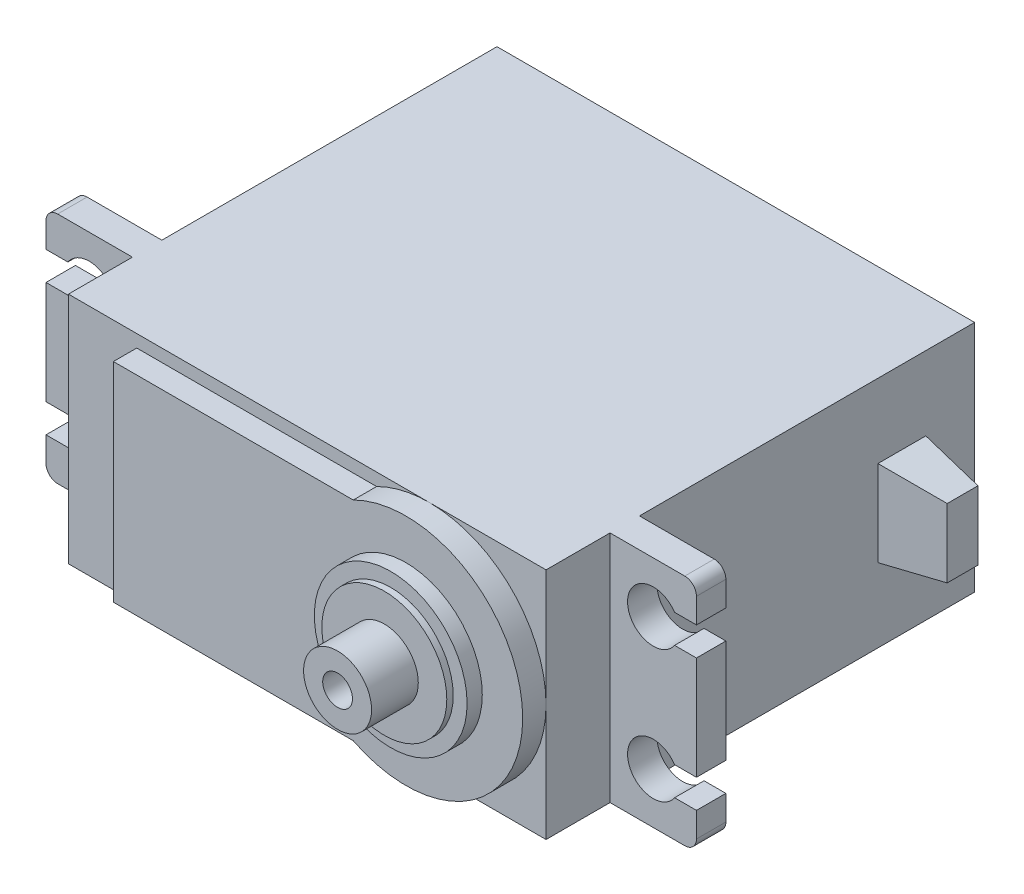
SolidWorks part; units mm, degrees
ref_plane "정면" through (0, 0, 0) normal (0, 0, 1) x (1, 0, 0)
ref_plane "윗면" through (0, 0, 0) normal (0, 1, 0) x (1, 0, 0)
ref_plane "우측면" through (0, 0, 0) normal (1, 0, 0) x (0, 0, -1)
sketch "스케치1" plane through (0, 0, 0) normal (0, 0, 1) x (1, 0, 0)
  line L1 (20.45, -10) -> (-20.45, -10)
  line L2 (20.45, -10) -> (20.45, 10)
  line L3 (20.45, 10) -> (-20.45, 10)
  line L4 (-20.45, -10) -> (-20.45, 10)
  line L5 (20.45, -10) -> (-20.45, 10) construction
  line L6 (20.45, 10) -> (-20.45, -10) construction
  point P0 (0, 0)
extrude "보스-돌출1" add sketch "스케치1" along normal blind 36.7
sketch "스케치2" plane through (0, 0, 36.7) normal (0, 0, 1) x (1, 0, 0)
  line L0 (20.45, -10) -> (20.45, 10) construction
  circle A0 centre (10.45, 0) radius 10
  dimension "D1" = 10
extrude "보스-돌출2" add sketch "스케치2" along normal blind 2
sketch "스케치3" plane through (0, 0, 38.7) normal (0, 0, 1) x (1, 0, 0)
  circle A0 centre (10.45, 0) radius 6.54
extrude "보스-돌출3" add sketch "스케치3" along normal blind 1.3
sketch "스케치4" plane through (0, 0, 40) normal (0, 0, 1) x (1, 0, 0)
  circle A0 centre (10.45, 0) radius 5.35
extrude "보스-돌출4" add sketch "스케치4" along normal blind 0.55
sketch "스케치5" plane through (0, 0, 40.55) normal (0, 0, 1) x (1, 0, 0)
  circle A1 centre (10.45, 0) radius 2.91
  circle A2 centre (10.45, 0) radius 1.275
extrude "보스-돌출5" add sketch "스케치5" along normal blind 4
sketch "스케치6" plane through (0, 0, 36.7) normal (0, 0, 1) x (1, 0, 0)
  line L0 (5.9395, 8.925) -> (-14.6, 8.925)
  line L1 (-14.6, 8.925) -> (-14.6, -8.925)
  line L2 (0.45, 0) -> (-14.6, 0) construction
  line L3 (5.9395, -8.925) -> (-14.6, -8.925)
  circle A0 centre (10.45, 0) radius 10 construction
  arc A2 (10.45, 10) -> (10.45, -10) centre (10.45, 0) ccw construction
  arc A3 (5.9395, 8.925) -> (5.9395, -8.925) centre (10.45, 0) ccw
  dimension "D1" = 5.85
  dimension "D2" = 17.85
extrude "보스-돌출6" add sketch "스케치6" along normal blind 2
sketch "스케치7" plane through (20.45, 0, 0) normal (1, 0, 0) x (0, 0, -1)
  line L0 (-36.7, -10) -> (0, -10) construction
  line L1 (-31.22, -10) -> (-28.7, -10)
  line L2 (-31.22, -10) -> (-31.22, 10)
  line L3 (-31.22, 10) -> (-28.7, 10)
  line L4 (-28.7, -10) -> (-28.7, 10)
  line L5 (-36.7, 10) -> (0, 10) construction
  line L6 (0, -10) -> (0, 10) construction
  dimension "D1" = 28.7
extrude "보스-돌출7" add sketch "스케치7" along normal blind 7.4
sketch "스케치8" plane through (0, 0, 31.22) normal (0, 0, 1) x (1, 0, 0)
  line L0 (27.85, 0) -> (20.45, 0) construction
  line L1 (27.85, 10) -> (27.85, -10) construction
  line L2 (20.45, 10) -> (20.45, -10) construction
  line L3 (24.15, 10) -> (24.15, 7.85) construction
  line L4 (27.85, 10) -> (20.45, 10) construction
  line L5 (27.85, 6.875) -> (27.85, 4.425)
  line L6 (27.85, -4.425) -> (27.85, -6.875)
  line L7 (27.85, 6.875) -> (25.9774, 6.875)
  line L9 (27.85, 4.425) -> (25.9774, 4.425)
  line L10 (27.85, -6.875) -> (25.9774, -6.875)
  line L11 (27.85, -4.425) -> (25.9774, -4.425)
  arc A0 (25.9774, 6.875) -> (25.9774, 4.425) centre (24.15, 5.65) ccw
  arc A1 (25.9774, -6.875) -> (25.9774, -4.425) centre (24.15, -5.65) cw
  dimension "D1" = 2.2
extrude "컷-돌출3" cut sketch "스케치8" against normal blind 3.4
fillet "필렛1" radius 1 2 edges at (27.85, 10, 29.96) (27.85, -10, 29.96)
mirror "대칭 복사1" about plane through (0, 0, 0) normal (1, 0, 0) of "필렛1", "컷-돌출3", "보스-돌출7"
sketch "스케치9" plane through (20.45, 0, 0) normal (1, 0, 0) x (0, 0, -1)
  line L0 (0, -10) -> (0, 10) construction
  line L1 (-8.28, -3.675) -> (-4.18, -3.675)
  line L2 (-8.28, -3.675) -> (-8.28, 3.675)
  line L3 (-8.28, 3.675) -> (-4.18, 3.675)
  line L4 (-4.18, -3.675) -> (-4.18, 3.675)
  line L5 (-8.28, -3.675) -> (-4.18, 3.675) construction
  line L6 (-8.28, 3.675) -> (-4.18, -3.675) construction
  line L7 (0, 0) -> (-14.4381, 0) construction
  point P0 (-6.23, 0)
  dimension "D1" = 7.35
  dimension "D2" = 4.1
  dimension "D3" = 4.18
  dimension "D4" = 0
extrude "보스-돌출8" add sketch "스케치9" along normal blind 5.2 draft 8
